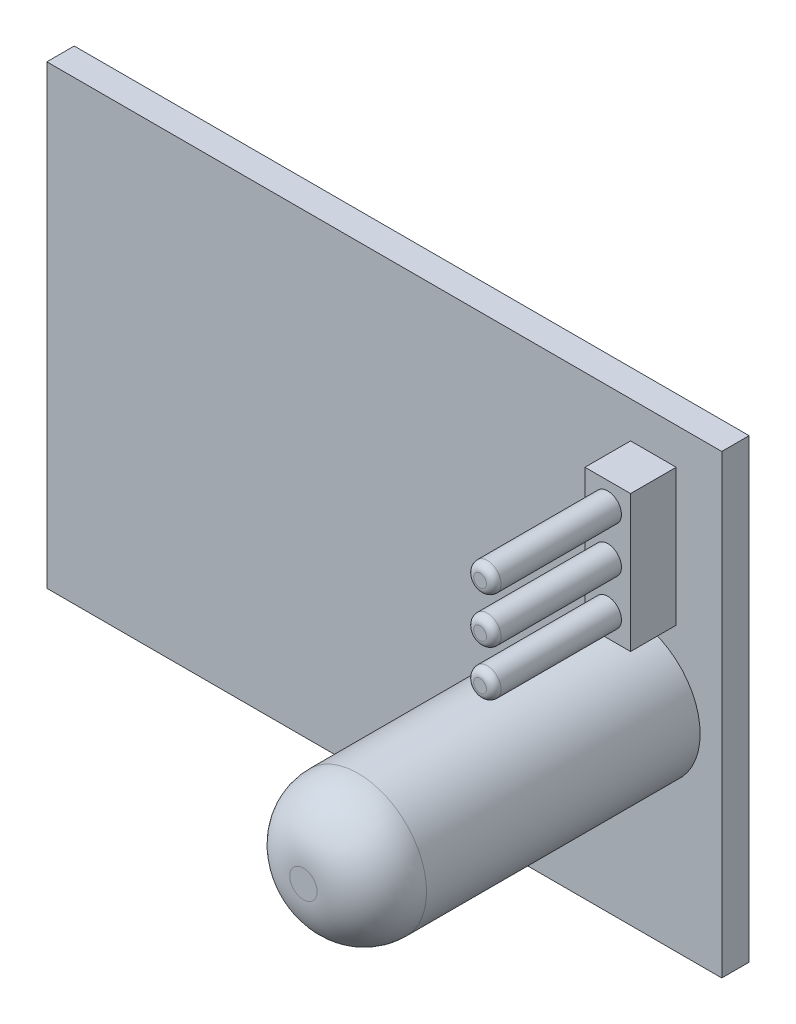
SolidWorks part; units mm, degrees
ref_plane "Ebene vorne" through (0, 0, 0) normal (0, 0, 1) x (1, 0, 0)
ref_plane "Ebene oben" through (0, 0, 0) normal (0, 1, 0) x (1, 0, 0)
ref_plane "Ebene rechts" through (0, 0, 0) normal (1, 0, 0) x (0, 0, -1)
sketch "Skizze1" plane through (0, 0, 0) normal (0, 0, 1) x (1, 0, 0)
  line L1 (18.5, -12.5) -> (-18.5, -12.5)
  line L2 (18.5, -12.5) -> (18.5, 12.5)
  line L3 (18.5, 12.5) -> (-18.5, 12.5)
  line L4 (-18.5, -12.5) -> (-18.5, 12.5)
  line L5 (18.5, -12.5) -> (-18.5, 12.5) construction
  line L6 (18.5, 12.5) -> (-18.5, -12.5) construction
  point P0 (0, 0)
  dimension "D1" = 37
  dimension "D2" = 25
extrude "Aufsatz-Linear austragen1" add sketch "Skizze1" along normal blind 1.5
sketch "Skizze3" plane through (0, 0, 1.5) normal (0, 0, 1) x (1, 0, 0)
  line L0 (-18.5, -12.5) -> (18.5, -12.5) construction
  circle A0 centre (13.5647, -1.5) radius 3.75
  dimension "D1" = 7.5
  dimension "D2" = 11
extrude "Aufsatz-Linear austragen2" add sketch "Skizze3" along normal blind 18
fillet "Verrundung1" radius 3 1 edges at (17.3147, -1.5, 19.5)
sketch "Skizze5" plane through (0, 0, 1.5) normal (0, 0, 1) x (1, 0, 0)
  line L0 (18.5, 12.5) -> (-18.5, 12.5) construction
  line L1 (13.5, 10.5) -> (16, 10.5)
  line L2 (13.5, 10.5) -> (13.5, 3)
  line L3 (13.5, 3) -> (16, 3)
  line L4 (16, 10.5) -> (16, 3)
  line L5 (13.5, 10.5) -> (16, 3) construction
  line L6 (13.5, 3) -> (16, 10.5) construction
  line L7 (18.5, -12.5) -> (18.5, 12.5) construction
  point P0 (14.75, 6.75)
  dimension "D1" = 2
  dimension "D2" = 7.5
  dimension "D3" = 2.5
  dimension "D4" = 2.5
extrude "Aufsatz-Linear austragen3" add sketch "Skizze5" along normal blind 2.5 separate body
sketch "Skizze6" plane through (0, 0, 4) normal (0, 0, 1) x (1, 0, 0)
  line L0 (16, 3) -> (16, 10.5) construction
  line L1 (16, 10.5) -> (13.5, 10.5) construction
  circle A0 centre (14.75, 9.25) radius 0.75
  dimension "D1" = 1.5
  dimension "D2" = 1.25
  dimension "D3" = 1.25
extrude "Aufsatz-Linear austragen4" add sketch "Skizze6" along normal blind 7
pattern_linear "Lineares Muster1" count 3 spacing 2.5 along (0, -1, 0) of "Aufsatz-Linear austragen4"
fillet "Verrundung2" radius 0.4 3 edges at (15.5, 9.25, 11) (15.5, 4.25, 11) (15.5, 6.75, 11)
